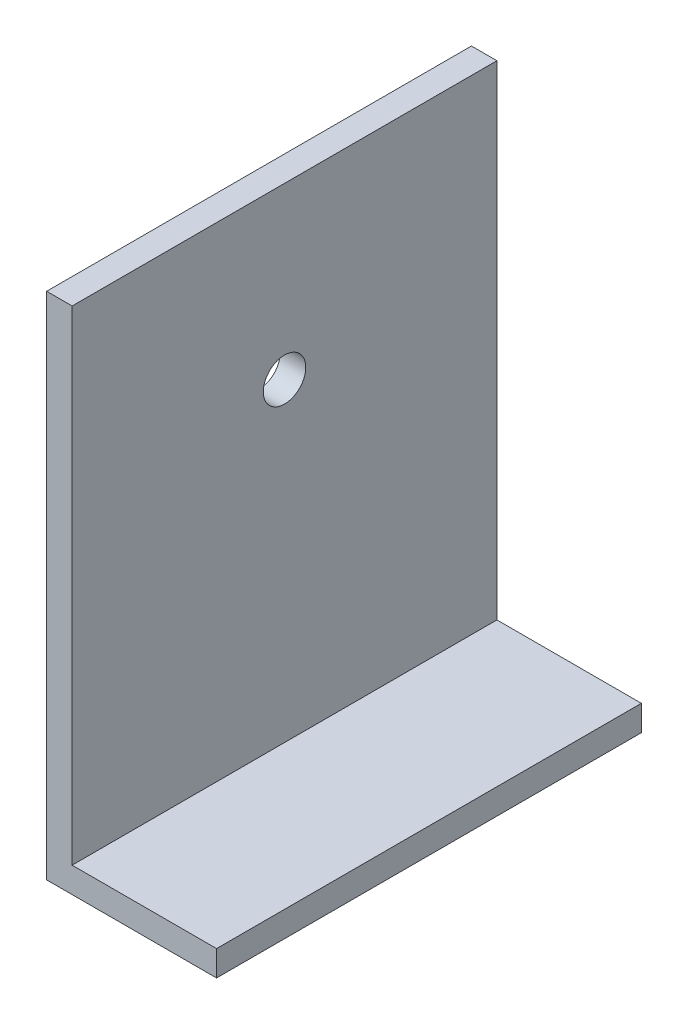
SolidWorks part; units mm, degrees
ref_plane "Front Plane" through (0, 0, 0) normal (0, 0, 1) x (1, 0, 0)
ref_plane "Top Plane" through (0, 0, 0) normal (0, 1, 0) x (1, 0, 0)
ref_plane "Right Plane" through (0, 0, 0) normal (1, 0, 0) x (0, 0, -1)
sketch "Sketch1" plane through (0, 0, 0) normal (0, 0, 1) x (1, 0, 0)
  line L1 (0, 0) -> (20, 0)
  line L2 (0, 0) -> (0, 60)
  line L3 (0, 60) -> (3, 60)
  line L4 (20, 0) -> (20, 3)
  line L7 (20, 3) -> (3, 3)
  line L8 (3, 60) -> (3, 3)
  dimension "D1" = 60
  dimension "D2" = 20
  dimension "D3" = 3
  dimension "D4" = 3
extrude "Boss-Extrude1" add sketch "Sketch1" along normal blind 50
sketch "Sketch2" plane through (0, 0, 0) normal (-1, 0, 0) x (0, 0, 1)
  line L0 (50, 0) -> (0, 0) construction
  circle A0 centre (25, 40) radius 2.5
  point P4 (0, 0)
  point P5 (0, 0)
  point P6 (25, 0)
  dimension "D2" = 5
  dimension "D1" = 40
extrude "Cut-Extrude1" cut sketch "Sketch2" against normal through all
